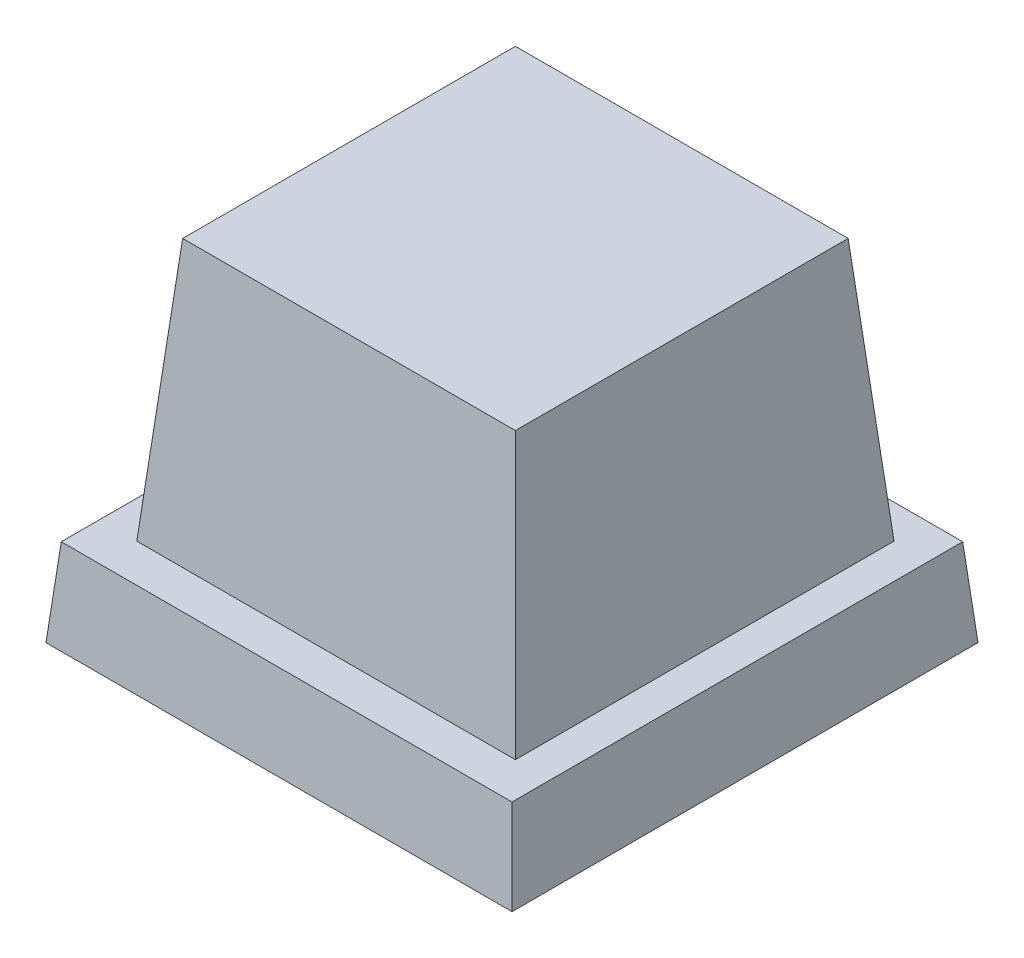
SolidWorks part; units mm, degrees
ref_plane "Front Plane" through (0, 0, 0) normal (0, 0, 1) x (1, 0, 0)
ref_plane "Top Plane" through (0, 0, 0) normal (0, 1, 0) x (1, 0, 0)
ref_plane "Right Plane" through (0, 0, 0) normal (1, 0, 0) x (0, 0, -1)
sketch "Sketch1" plane through (0, 0, 0) normal (0, 1, 0) x (1, 0, 0)
  line L13 (0, 0) -> (-32, 0)
  line L14 (0, 0) -> (0, 32)
  line L15 (0, 32) -> (-32, 32)
  line L16 (-32, 0) -> (-32, 32)
  dimension "D1" = 32
  dimension "D2" = 32
extrude "Boss-Extrude1" add sketch "Sketch1" along normal blind 6 draft 5
sketch "Sketch2" plane through (0, 6, 0) normal (0, 1, 0) x (1, 0, 0)
  line L1 (-28.9231, 29.1567) -> (-2.9231, 29.1567)
  line L2 (-28.9231, 29.1567) -> (-28.9231, 3.1567)
  line L3 (-28.9231, 3.1567) -> (-2.9231, 3.1567)
  line L4 (-2.9231, 29.1567) -> (-2.9231, 3.1567)
  point P4 (-29.5843, 29.5228)
  dimension "D1" = 26
  dimension "D2" = 26
extrude "Boss-Extrude2" add sketch "Sketch2" along normal blind 18 draft 5
shell "Shell1" thickness 0.8
equation "\"D2@Sketch1\"=\"D1@Sketch1\""
equation "\"D2@Sketch2\"=\"D1@Sketch2\""
